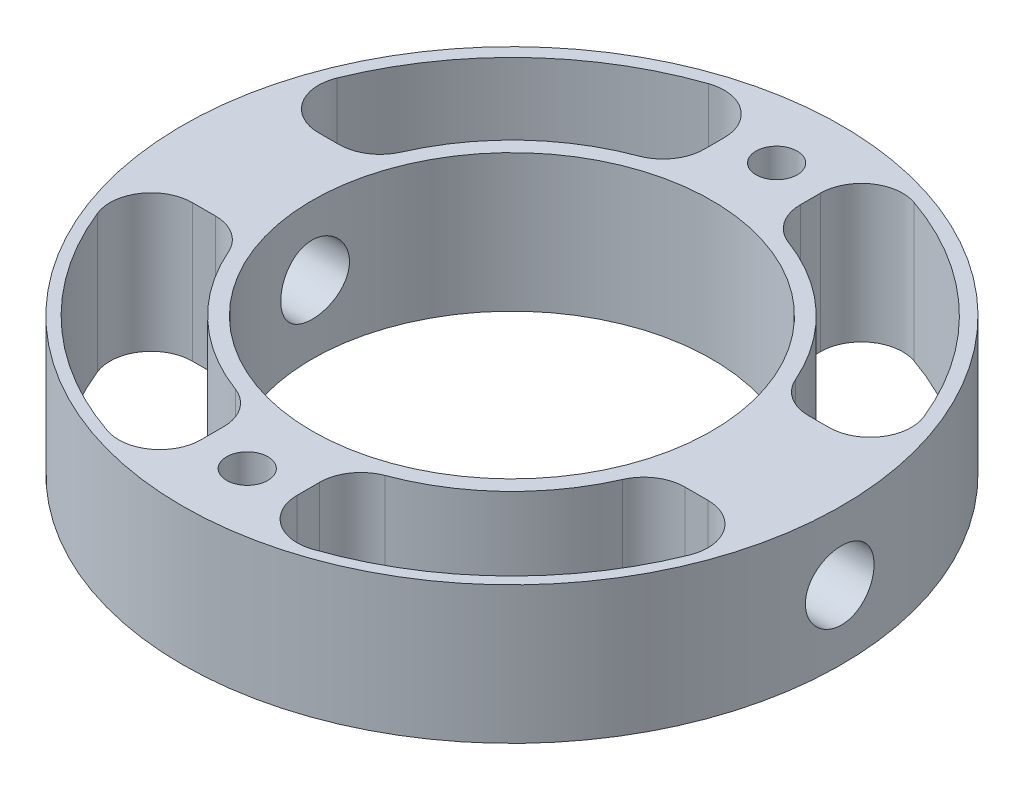
SolidWorks part; units mm, degrees
ref_plane "Front Plane" through (0, 0, 0) normal (0, 0, 1) x (1, 0, 0)
ref_plane "Top Plane" through (0, 0, 0) normal (0, 1, 0) x (1, 0, 0)
ref_plane "Right Plane" through (0, 0, 0) normal (1, 0, 0) x (0, 0, -1)
sketch "Sketch3" plane through (0, 0, 0) normal (0, 1, 0) x (1, 0, 0)
  circle A0 centre (0, 0) radius 24
  circle A1 centre (0, 0) radius 14.55
  dimension "D1" = 48
  dimension "D2" = 29.1
extrude "Boss-Extrude1" add sketch "Sketch3" along normal blind 10
sketch "Sketch4" plane through (0, 0, 0) normal (1, 0, 0) x (0, 0, -1)
  circle A0 centre (0, 5) radius 2.5
  dimension "D1" = 5
  dimension "D2" = 5
extrude "Cut-Extrude2" cut sketch "Sketch4" against normal blind 100 from offset 50
sketch "Sketch5" plane through (0, 10, 0) normal (0, 1, 0) x (1, 0, 0)
  circle A0 centre (0, 19.275) radius 1.5
  circle A3 centre (0, -19.275) radius 1.5
  dimension "D1" = 3
  dimension "D4" = 3
  dimension "D2" = 19.275
  dimension "D3" = 19.275
extrude "Cut-Extrude3" cut sketch "Sketch5" against normal blind 100
sketch "Sketch7" plane through (0, 10, 0) normal (0, 1, 0) x (1, 0, 0)
  line L0 (3.5, 15.275) -> (3.5, 22.775)
  line L1 (15.0109, 4.5) -> (22.5987, 4.5)
  arc A0 (3.5, 22.775) -> (22.5987, 4.5) centre (0, 0) cw
  arc A1 (3.5, 15.275) -> (15.0109, 4.5) centre (0, 0) cw
  dimension "D1" = 3.5
  dimension "D2" = 22.775
  dimension "D4" = 4.5
  dimension "D3" = 3.5
  dimension "D5" = 15.275
  dimension "D6" = 4.5
extrude "Cut-Extrude6" cut sketch "Sketch7" against normal blind 26
sketch "Sketch9" plane through (0, 10, 0) normal (0, 1, 0) x (1, 0, 0)
  line L0 (15.0109, -4.5) -> (22.775, -4.5)
  line L1 (3.5, -15.275) -> (3.5, -22.95)
  arc A0 (15.0109, -4.5) -> (3.5, -15.275) centre (0, 0) cw
  arc A1 (22.775, -4.5) -> (3.5, -22.95) centre (0, 0) cw
  dimension "D2" = 4.5
  dimension "D3" = 4.5
  dimension "D4" = 22.775
  dimension "D5" = 3.5
  dimension "D6" = 3.5
  dimension "D1" = 15.275
extrude "Cut-Extrude7" cut sketch "Sketch9" against normal blind 26
sketch "Sketch10" plane through (0, 10, 0) normal (0, 1, 0) x (1, 0, 0)
  line L0 (-3.5, 15.275) -> (-3.5, 22.775)
  line L1 (-22.5987, 4.5) -> (-15.0109, 4.5)
  arc A0 (-3.5, 15.275) -> (-15.0109, 4.5) centre (0, 0) ccw
  arc A1 (-3.5, 22.775) -> (-22.5987, 4.5) centre (0, 0) ccw
  dimension "D1" = 3.5
  dimension "D6" = 4.5
  dimension "D3" = 4.5
  dimension "D2" = 15.275
  dimension "D4" = 3.5
  dimension "D5" = 22.775
extrude "Cut-Extrude8" cut sketch "Sketch10" against normal blind 26
sketch "Sketch11" plane through (0, 10, 0) normal (0, 1, 0) x (1, 0, 0)
  line L0 (-15.0109, -4.5) -> (-22.775, -4.5)
  line L1 (-3.5, -15.275) -> (-3.5, -22.95)
  arc A0 (-22.775, -4.5) -> (-3.5, -22.95) centre (0, 0) ccw
  arc A1 (-3.5, -15.275) -> (-15.0109, -4.5) centre (0, 0) cw
  dimension "D4" = 4.5
  dimension "D3" = 3.5
  dimension "D2" = 4.5
  dimension "D5" = 3.5
  dimension "D1" = 22.775
  dimension "D6" = 15.275
extrude "Cut-Extrude9" cut sketch "Sketch11" against normal blind 26
fillet "Fillet5" radius 3 16 edges at (3.5, 5, -15.275) (3.5, 5, -22.775) (15.0109, 5, -4.5) (22.5987, 5, -4.5) (15.0109, 5, 4.5) (22.775, 5, 4.5) (3.5, 5, 15.275) (3.5, 5, 22.95) (-3.5, 5, 22.95) (-3.5, 5, 15.275) (-22.775, 5, 4.5) (-15.0109, 5, 4.5) (-15.0109, 5, -4.5) (-22.5987, 5, -4.5) (-3.5, 5, -15.275) (-3.5, 5, -22.775)
equation "\"TubeInnerDiameter\"= 48mm"
equation "\"MotorCasingDiameter\"= 29.1mm"
equation "\"BoltDiameter\"= 5mm"
equation "\"SpacerHeight\"= 10mm"
equation "\"D1@Sketch3\"=\"TubeInnerDiameter\""
equation "\"D1@Boss-Extrude1\"=\"SpacerHeight\""
equation "\"D1@Sketch4\"=\"BoltDiameter\""
equation "\"D2@Sketch4\"=\"SpacerHeight\"/2"
equation "\"TopBoltDiameter\"= 3mm"
equation "\"D1@Sketch5\"=\"TopBoltDiameter\""
equation "\"D2@Sketch5\"=(\"TubeInnerDiameter\"/2-\"MotorCasingDiameter\"/2)/2+\"MotorCasingDiameter\"/2"
equation "\"D4@Sketch5\"=\"TopBoltDiameter\""
equation "\"D3@Sketch5\"=(\"TubeInnerDiameter\"/2-\"MotorCasingDiameter\"/2)/2+\"MotorCasingDiameter\"/2"
equation "\"PressureChannelWidth\"= 8mm"
equation "\"IgniterChannelDiameter\"= 2.8mm"
equation "\"D1@Sketch7\"=\"TopBoltDiameter\"/2+\"BoltChannelSeparation\""
equation "\"D4@Sketch7\"=\"BoltDiameter\"/2+\"BoltChannelSeparation\""
equation "\"BoltChannelSeparation\"= 2mm"
equation "\"D3@Sketch7\"=\"TopBoltDiameter\"/2+\"BoltChannelSeparation\""
equation "\"D5@Sketch7\"=(\"TubeInnerDiameter\"/2+\"MotorCasingDiameter\"/2)/2-\"PressureChannelWidth\"/2"
equation "\"D6@Sketch7\"=\"BoltDiameter\"/2+\"BoltChannelSeparation\""
equation "\"D2@Sketch7\"=(\"TubeInnerDiameter\"/2+\"MotorCasingDiameter\"/2)/2+\"PressureChannelWidth\"/2-0.5"
equation "\"D2@Sketch3\"=\"MotorCasingDiameter\""
equation "\"ChamferRadius\"= 3mm"
equation "\"D2@Sketch9\"=\"BoltDiameter\"/2+\"BoltChannelSeparation\""
equation "\"D3@Sketch9\"=\"BoltDiameter\"/2+\"BoltChannelSeparation\""
equation "\"D4@Sketch9\"=(\"TubeInnerDiameter\"/2+\"MotorCasingDiameter\"/2)/2+\"PressureChannelWidth\"/2-0.5mm"
equation "\"D5@Sketch9\"=\"TopBoltDiameter\"/2+\"BoltChannelSeparation\""
equation "\"D6@Sketch9\"=\"TopBoltDiameter\"/2+\"BoltChannelSeparation\""
equation "\"D1@Sketch10\"=\"TopBoltDiameter\"/2+\"BoltChannelSeparation\""
equation "\"D2@Sketch10\"=(\"TubeInnerDiameter\"/2+\"MotorCasingDiameter\"/2)/2-\"PressureChannelWidth\"/2"
equation "\"D3@Sketch10\"=\"BoltDiameter\"/2+\"BoltChannelSeparation\""
equation "\"D4@Sketch10\"=\"TopBoltDiameter\"/2+\"BoltChannelSeparation\""
equation "\"D5@Sketch10\"=(\"TubeInnerDiameter\"/2+\"MotorCasingDiameter\"/2)/2+\"PressureChannelWidth\"/2-0.5mm"
equation "\"D6@Sketch10\"=\"BoltDiameter\"/2+\"BoltChannelSeparation\""
equation "\"D1@Sketch11\"=(\"TubeInnerDiameter\"/2+\"MotorCasingDiameter\"/2)/2+\"PressureChannelWidth\"/2-0.5mm"
equation "\"D2@Sketch11\"=\"BoltDiameter\"/2+\"BoltChannelSeparation\""
equation "\"D3@Sketch11\"=\"TopBoltDiameter\"/2+\"BoltChannelSeparation\""
equation "\"D4@Sketch11\"=\"BoltDiameter\"/2+\"BoltChannelSeparation\""
equation "\"D5@Sketch11\"=\"TopBoltDiameter\"/2+\"BoltChannelSeparation\""
equation "\"D6@Sketch11\"=(\"TubeInnerDiameter\"/2+\"MotorCasingDiameter\"/2)/2-\"PressureChannelWidth\"/2"
equation "\"D1@Fillet5\"=\"ChamferRadius\""
equation "\"D1@Sketch9\"=(\"TubeInnerDiameter\"/2+\"MotorCasingDiameter\"/2)/2-\"PressureChannelWidth\"/2"
